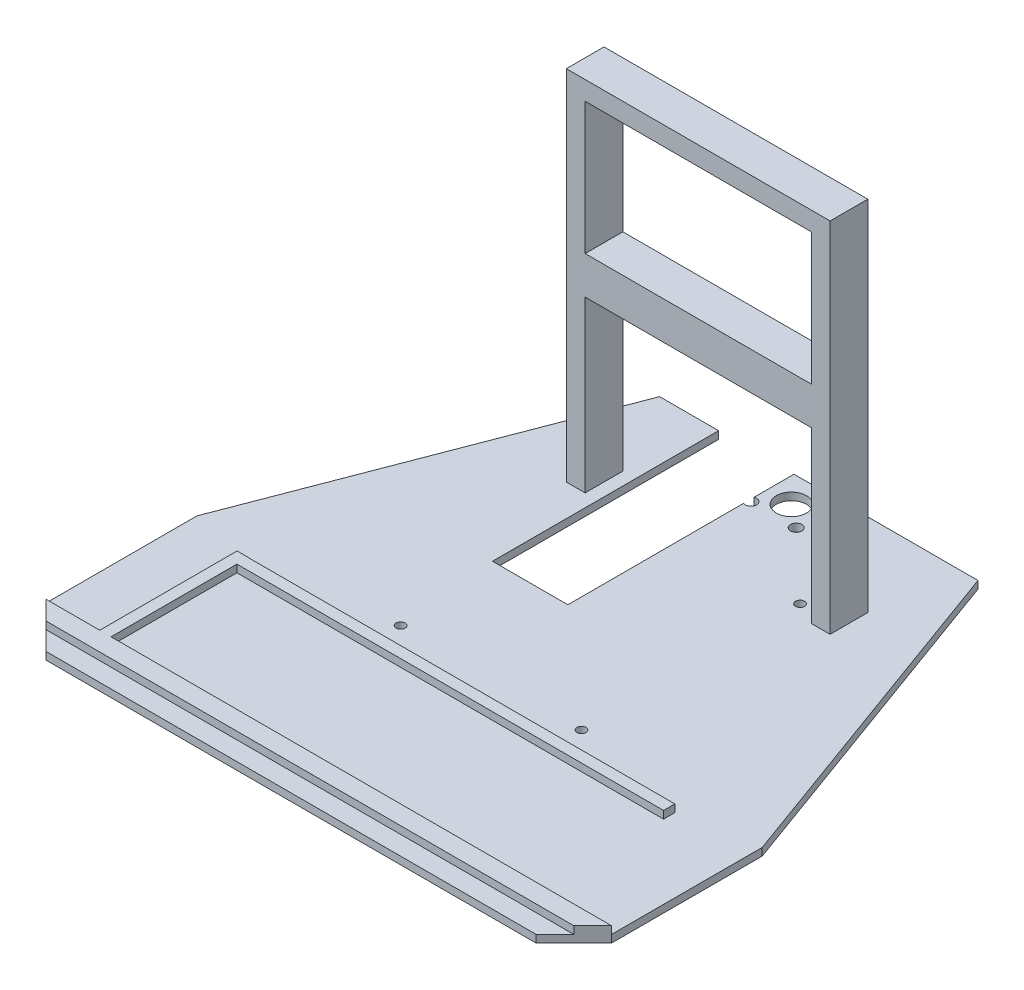
SolidWorks part; units mm, degrees
ref_plane "Front Plane" through (0, 0, 0) normal (0, 0, 1) x (1, 0, 0)
ref_plane "Top Plane" through (0, 0, 0) normal (0, 1, 0) x (1, 0, 0)
ref_plane "Right Plane" through (0, 0, 0) normal (1, 0, 0) x (0, 0, -1)
sketch "Sketch1" plane through (0, 0, 0) normal (0, 1, 0) x (1, 0, 0)
  line L0 (-76.1909, -68.8761) -> (-65.067, -80)
  line L1 (-65.067, -80) -> (65, -80)
  line L2 (-76.1909, -68.8761) -> (-76.1909, -28.8187)
  line L3 (-42.2121, 59.9681) -> (42.2843, 59.9681)
  line L4 (75, -70) -> (75, -30)
  line L5 (-74.9952, -78.8044) -> (76.6113, 80.5025) construction
  line L6 (-76.1172, 81.1917) -> (75, -80) construction
  line L7 (75, -70) -> (65, -80)
  line L8 (-76.1909, -28.8187) -> (-42.2121, 59.9681)
  line L9 (42.2843, 59.9681) -> (75, -30)
  point P0 (0, 0)
  point P14 (-42.3824, 59.6985)
  point P15 (0, 0)
  point P16 (0, 0)
  point P17 (42.2843, 59.9681)
  dimension "D1" = 160
  dimension "D2" = 150
  dimension "D3" = 10
  dimension "D4" = 10
  dimension "D5" = 10
  dimension "D6" = 10
  dimension "D7" = 50
  dimension "D8" = 50
  dimension "D9" = 40
  dimension "40" = 40
extrude "Boss-Extrude1" add sketch "Sketch1" along normal blind 2
sketch "Sketch2" plane through (0, 2, 0) normal (0, 1, 0) x (1, 0, 0)
  line L0 (-75.067, -70) -> (75, -70)
  line L3 (75, -70) -> (75, -30) construction
  line L4 (75, -70) -> (70, -75)
  line L5 (65, -80) -> (75, -70) construction
  line L6 (70, -75) -> (-70.067, -75)
  line L7 (-70.067, -75) -> (-75.067, -70)
  line L8 (-76.1909, -68.8761) -> (-65.067, -80) construction
extrude "Boss-Extrude2" add sketch "Sketch2" along normal blind 2
sketch "Sketch3" plane through (0, 2, 0) normal (0, 1, 0) x (1, 0, 0)
  line L0 (0.0361, -70) -> (0.0361, 59.9681) construction
  line L2 (42.2843, 59.9681) -> (-42.2121, 59.9681) construction
  line L3 (-76.1909, -30) -> (75, -30) construction
  line L4 (-76.1909, -28.8187) -> (-76.1909, -68.8761) construction
  line L5 (75, -70) -> (75, -30) construction
sketch "Sketch4" plane through (0, 2, 0) normal (0, 1, 0) x (1, 0, 0)
  line L0 (-57.8009, -70) -> (-57.8009, -33.56)
  line L1 (75, -70) -> (-75.067, -70) construction
  line L2 (-57.8009, -33.56) -> (-60.8009, -33.56)
  line L3 (-60.8009, -33.56) -> (-60.8009, -70)
  line L4 (-60.8009, -70) -> (-57.8009, -70)
  line L5 (-76.1909, -28.8187) -> (-76.1909, -68.8761) construction
  point P8 (-59.3009, -70)
  dimension "D1" = 3
  dimension "D2" = 18.39
  dimension "D3" = 36.44
extrude "Boss-Extrude3" add sketch "Sketch4" along normal blind 2
sketch "Sketch5" plane through (0, 2, 0) normal (0, 1, 0) x (1, 0, 0)
  line L0 (-57.8009, -36.6) -> (55.4191, -36.6)
  line L1 (-57.8009, -70) -> (-57.8009, -33.56) construction
  line L2 (55.4191, -36.6) -> (55.4191, -33.6)
  line L3 (55.4191, -33.6) -> (-57.8009, -33.6)
  line L4 (-57.8009, -33.6) -> (-57.8009, -36.6)
  line L5 (75, -70) -> (-57.8009, -70) construction
  dimension "D1" = 3
  dimension "D2" = 33.4
  dimension "D3" = 113.22
extrude "Boss-Extrude4" add sketch "Sketch5" along normal blind 2
sketch "Sketch6" plane through (0, 2, 0) normal (0, 1, 0) x (1, 0, 0)
  line L1 (-76.1909, -30) -> (75, -30) construction
  line L2 (0.0361, -70) -> (0.0361, 59.9681) construction
  circle A0 centre (-23.9639, 31) radius 1.2
  circle A1 centre (24.0361, 31) radius 1.2
  circle A2 centre (-23.9639, -27) radius 1.2
  circle A3 centre (24.0361, -27) radius 1.2
  dimension "D1" = 2.4
  dimension "D2" = 2.4
  dimension "D3" = 2.4
  dimension "D4" = 2.4
  dimension "D5" = 48
  dimension "D6" = 24
  dimension "D7" = 58
  dimension "D8" = 3
extrude "Cut-Extrude1" cut sketch "Sketch6" against normal up to next
sketch "Sketch8" plane through (0, 0, 0) normal (0, -1, 0) x (1, 0, 0)
  line L0 (-42.2121, -59.9681) -> (42.2843, -59.9681)
  line L1 (-42.2121, -59.9681) -> (-76.1909, 28.8187) construction
  line L2 (42.2843, -59.9681) -> (-42.2121, -59.9681) construction
  line L3 (42.2843, -59.9681) -> (43.3752, -56.9681)
  line L4 (75, 30) -> (42.2843, -59.9681) construction
  line L5 (43.3752, -56.9681) -> (-43.3602, -56.9681)
  line L6 (-43.3602, -56.9681) -> (-42.2121, -59.9681)
  dimension "D1" = 3
sketch "Sketch10" plane through (0, 2, 0) normal (0, 1, 0) x (1, 0, 0)
  line L0 (0.0361, -70) -> (0.0361, 59.9681) construction
  line L1 (42.2843, 59.9681) -> (-42.2121, 59.9681) construction
  circle A0 centre (-5.9639, 47.9681) radius 1.5
  circle A1 centre (6.0361, 47.9681) radius 1.5
  dimension "D1" = 3
  dimension "D2" = 3
  dimension "D3" = 12
  dimension "D4" = 6
  dimension "D5" = 12
extrude "Cut-Extrude2" cut sketch "Sketch10" against normal up to next
sketch "Sketch11" plane through (0, 2, 0) normal (0, 1, 0) x (1, 0, 0)
  line L0 (42.2843, 59.9681) -> (-42.2121, 59.9681) construction
  line L1 (-34.9639, 27.9681) -> (-29.9639, 27.9681)
  line L2 (-34.9639, 27.9681) -> (-34.9639, 37.9681)
  line L3 (-34.9639, 37.9681) -> (-29.9639, 37.9681)
  line L4 (-29.9639, 27.9681) -> (-29.9639, 37.9681)
  line L5 (30.0361, 27.9681) -> (35.0361, 27.9681)
  line L6 (30.0361, 27.9681) -> (30.0361, 37.9681)
  line L7 (30.0361, 37.9681) -> (35.0361, 37.9681)
  line L8 (35.0361, 27.9681) -> (35.0361, 37.9681)
  line L9 (0.0361, -70) -> (0.0361, 59.9681) construction
  dimension "D1" = 5
  dimension "D2" = 10
  dimension "D3" = 10
  dimension "D4" = 5
  dimension "D5" = 22
  dimension "D6" = 32
  dimension "D7" = 30
  dimension "D8" = 30
extrude "Boss-Extrude6" add sketch "Sketch11" along normal blind 95
sketch "Sketch12" plane through (-29.9639, 0, 0) normal (1, 0, 0) x (0, 0, -1)
  line L0 (27.9681, 97) -> (37.9681, 97) construction
  line L1 (27.9681, 97) -> (37.9681, 97)
  line L2 (27.9681, 97) -> (27.9681, 92)
  line L3 (27.9681, 92) -> (37.9681, 92)
  line L4 (37.9681, 97) -> (37.9681, 92)
  line L5 (27.9681, 97) -> (27.9681, 2) construction
  line L6 (37.9681, 97) -> (37.9681, 2) construction
  dimension "D1" = 5
extrude "Boss-Extrude7" add sketch "Sketch12" along normal blind 60
sketch "Sketch13" plane through (0, 97, 0) normal (0, 1, 0) x (1, 0, 0)
  line L0 (0.0361, -70) -> (0.0361, 59.9681) construction
  line L1 (-34.9639, 37.9681) -> (-34.9639, 27.9681) construction
  circle A0 centre (0.0361, 52.7047) radius 4
  dimension "D1" = 8
  dimension "D2" = 35
extrude "Cut-Extrude3" cut sketch "Sketch13" against normal up to next
sketch "Sketch14" plane through (-29.9639, 0, 0) normal (1, 0, 0) x (0, 0, -1)
  line L0 (27.9681, 92) -> (27.9681, 2) construction
  line L1 (27.9681, 57) -> (37.9681, 57)
  line L2 (27.9681, 57) -> (27.9681, 47)
  line L3 (27.9681, 47) -> (37.9681, 47)
  line L4 (37.9681, 57) -> (37.9681, 47)
  line L5 (37.9681, 92) -> (37.9681, 2) construction
  line L6 (27.9681, 2) -> (37.9681, 2) construction
  dimension "D1" = 10
  dimension "D2" = 45
extrude "Boss-Extrude8" add sketch "Sketch14" along normal blind 60
sketch "Sketch16" plane through (0, 2, 0) normal (0, 1, 0) x (1, 0, 0)
  line L0 (42.2843, 59.9681) -> (-42.2121, 59.9681) construction
  line L1 (-26.5506, 59.9681) -> (-6.5506, 59.9681)
  line L2 (-26.5506, 59.9681) -> (-26.5506, -0.0319)
  line L3 (-26.5506, -0.0319) -> (-6.5506, -0.0319)
  line L4 (-6.5506, 59.9681) -> (-6.5506, -0.0319)
  dimension "D1" = 20
  dimension "D2" = 60
extrude "Cut-Extrude4" cut sketch "Sketch16" against normal up to next
